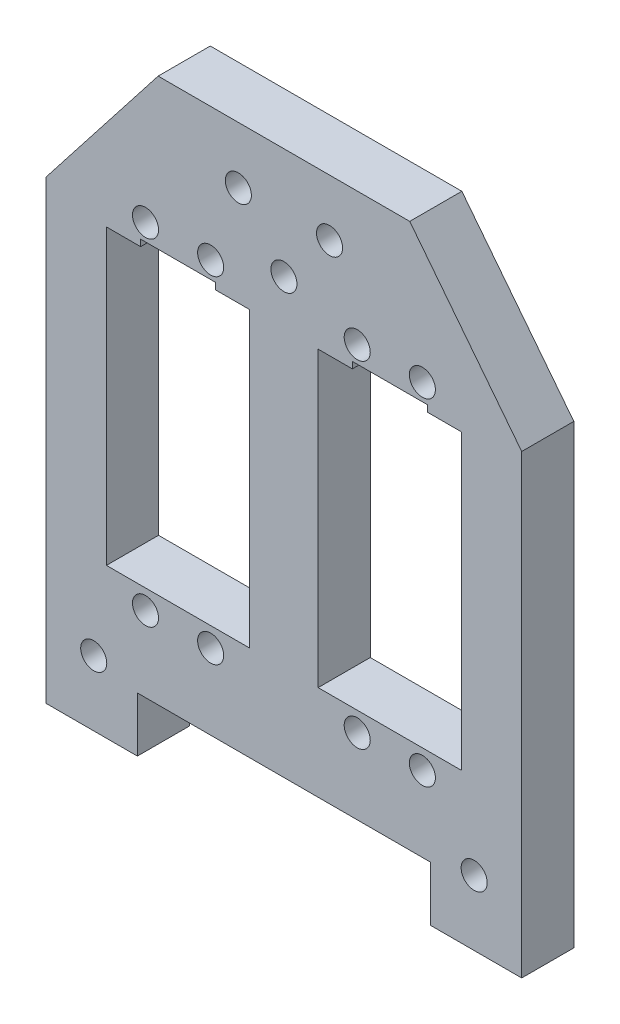
SolidWorks part; units mm, degrees
ref_plane "Plano frontal" through (0, 0, 0) normal (0, 0, 1) x (1, 0, 0)
ref_plane "Plano superior" through (0, 0, 0) normal (0, 1, 0) x (1, 0, 0)
ref_plane "Plano direito" through (0, 0, 0) normal (1, 0, 0) x (0, 0, -1)
sketch "Esboço1" plane through (0, 0, 0) normal (0, 0, 1) x (1, 0, 0)
  line L0 (-27.2502, -29.5201) -> (-27.2502, -7.0201)
  line L1 (-27.2502, -29.5201) -> (-27.2502, -52.0201)
  line L2 (-5.2502, -29.5201) -> (-5.2502, -52.0201)
  line L3 (-5.2502, -29.5201) -> (-5.2502, -7.0201)
  line L4 (16.2502, -3.4201) -> (21.2502, -3.4201) construction
  line L5 (16.2502, -7.0201) -> (16.2502, -3.4201) construction
  line L6 (27.2502, -7.0201) -> (5.2502, -7.0201) construction
  line L7 (22.0002, -7.0201) -> (22.0622, -6.9785) construction
  line L8 (-16.2502, -52.0201) -> (-16.2502, -55.0199) construction
  line L9 (16.2502, -55.0199) -> (21.2502, -55.0199) construction
  line L10 (5.2502, -29.5201) -> (27.2502, -29.5201) construction
  line L11 (16.2502, -52.0201) -> (16.2502, -55.0199) construction
  line L12 (10.5002, -7.0201) -> (5.2502, -7.0201)
  line L13 (-22.0002, -7.0201) -> (-22.0002, -6.0201)
  line L14 (-22.0002, -6.0201) -> (-10.5002, -6.0201)
  line L15 (-10.5002, -6.0201) -> (-10.5002, -7.0201)
  line L16 (0, -66.6) -> (0, 0) construction
  line L17 (-27.2502, -52.0201) -> (-5.2502, -52.0201)
  line L18 (-27.2502, -7.0201) -> (-22.0002, -7.0201)
  line L19 (27.2502, -7.0201) -> (22.0002, -7.0201)
  line L20 (19.3117, 17) -> (-19.3117, 17)
  line L21 (-19.3117, 17) -> (-36.5, -5)
  line L22 (-36.5, -5) -> (-36.5, -75)
  line L23 (-36.5, -75) -> (-22.5, -75)
  line L24 (-22.5, -75) -> (-22.5, -66.6)
  line L25 (-22.5, -66.6) -> (22.5, -66.6)
  line L26 (22.5, -66.6) -> (22.5, -75)
  line L27 (22.5, -75) -> (36.5, -75)
  line L28 (36.5, -75) -> (36.5, -5)
  line L29 (36.5, -5) -> (19.3117, 17)
  line L30 (27.2502, -52.0201) -> (5.2502, -52.0201)
  line L31 (10.5002, -6.0201) -> (10.5002, -7.0201)
  line L32 (-5.2502, -29.5201) -> (-27.2502, -29.5201) construction
  line L33 (-10.5002, -7.0201) -> (-5.2502, -7.0201)
  line L34 (-16.2502, -55.0199) -> (-21.2502, -55.0199) construction
  line L35 (-22.0002, -7.0201) -> (-22.0622, -6.9785) construction
  line L36 (22.0002, -6.0201) -> (10.5002, -6.0201)
  line L37 (-27.2502, -7.0201) -> (-5.2502, -7.0201) construction
  line L38 (-16.2502, -7.0201) -> (-16.2502, -3.4201) construction
  line L39 (-16.2502, -3.4201) -> (-21.2502, -3.4201) construction
  line L40 (22.0002, -7.0201) -> (22.0002, -6.0201)
  line L41 (5.2502, -29.5201) -> (5.2502, -7.0201)
  line L42 (5.2502, -29.5201) -> (5.2502, -52.0201)
  line L43 (27.2502, -29.5201) -> (27.2502, -52.0201)
  line L44 (27.2502, -29.5201) -> (27.2502, -7.0201)
  circle A0 centre (-21.2502, -3.4201) radius 2
  circle A1 centre (-11.2502, -55.0199) radius 2
  circle A2 centre (0, 0) radius 2.1419 construction
  circle A3 centre (11.2502, -3.4201) radius 2
  circle A4 centre (21.2502, -55.0199) radius 2
  circle A5 centre (-21.2502, -55.0199) radius 2
  circle A6 centre (-11.2502, -3.4201) radius 2
  circle A7 centre (11.2502, -55.0199) radius 2
  circle A8 centre (21.2502, -3.4201) radius 2
  circle A9 centre (29.2106, -64.8816) radius 2.1375 construction
  circle A10 centre (-28.815, -64.9968) radius 2.1336 construction
  circle A13 centre (0, 0) radius 2
  circle A14 centre (-7, 8.3) radius 2
  circle A15 centre (7, 8.3) radius 2
  circle A20 centre (-29.2, -65) radius 2
  circle A21 centre (29.2, -65) radius 2
  point P18 (0, -52.0201)
  point P20 (0, -52.0201)
extrude "Ressalto-extrusão1" add sketch "Esboço1" along normal blind 8
